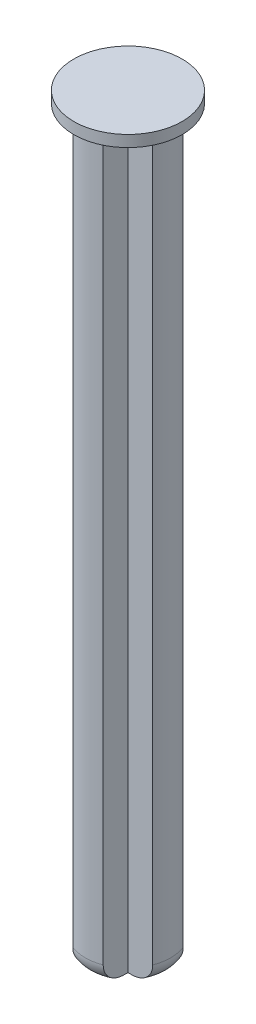
SolidWorks part; units mm, degrees
ref_plane "Front Plane" through (0, 0, 0) normal (0, 0, 1) x (1, 0, 0)
ref_plane "Top Plane" through (0, 0, 0) normal (0, 1, 0) x (1, 0, 0)
ref_plane "Right Plane" through (0, 0, 0) normal (1, 0, 0) x (0, 0, -1)
sketch "Sketch1" plane through (0, 0, 0) normal (0, 1, 0) x (1, 0, 0)
  line L0 (-0.8, -0.8) -> (-0.8, -2.103)
  line L1 (-0.8, 0.8) -> (-2.103, 0.8)
  line L2 (2.103, 0.8) -> (0.8, 0.8)
  line L3 (2.103, -0.8) -> (0.8, -0.8)
  line L4 (0.8, -0.8) -> (0.8, -2.103)
  line L5 (-0.8, -0.8) -> (-2.103, -0.8)
  line L6 (-7.75, 0) -> (-7.75, 0)
  line L7 (-7.75, 0) -> (-7.75, 0)
  line L8 (-0.8, 2.103) -> (-0.8, 0.8)
  line L9 (0.8, 2.103) -> (0.8, 0.8)
  line L10 (-7.75, 0) -> (-7.75, 0)
  line L11 (7.75, 0) -> (7.75, 0)
  line L12 (7.75, 0) -> (7.75, 0)
  line L13 (7.75, 0) -> (7.75, 0)
  line L14 (7.75, 0) -> (7.75, 0)
  line L15 (-7.75, 0) -> (-7.75, 0)
  line L16 (-8.6621, 8.6621) -> (-8.6621, 8.6621)
  line L17 (-8.6621, -8.6621) -> (-8.6621, -8.6621)
  line L18 (-8.6621, -8.6621) -> (-8.6621, -8.6621)
  line L19 (8.6621, -8.6621) -> (8.6621, -8.6621)
  line L20 (8.6621, -8.6621) -> (8.6621, -8.6621)
  line L21 (8.6621, 8.6621) -> (8.6621, 8.6621)
  line L22 (8.6621, 8.6621) -> (8.6621, 8.6621)
  line L23 (-8.6621, 8.6621) -> (-8.6621, 8.6621)
  arc A0 (-2.103, 0.8) -> (-2.103, -0.8) centre (0, 0) ccw
  arc A1 (0.8, 2.103) -> (-0.8, 2.103) centre (0, 0) ccw
  arc A2 (2.103, -0.8) -> (2.103, 0.8) centre (0, 0) ccw
  arc A3 (-0.8, -2.103) -> (0.8, -2.103) centre (0, 0) ccw
  arc A4 (-7.75, 0) -> (-7.75, 0) centre (-7.75, 0) ccw
  arc A5 (-7.75, 0) -> (7.75, 0) centre (0, 0) ccw
  arc A6 (7.75, 0) -> (7.75, 0) centre (7.75, 0) ccw
  arc A7 (7.75, 0) -> (-7.75, 0) centre (0, 0) ccw
  arc A8 (-8.6621, 8.6621) -> (-8.6621, -8.6621) centre (0, 0) ccw
  arc A9 (-8.6621, -8.6621) -> (8.6621, -8.6621) centre (0, 0) ccw
  arc A10 (8.6621, -8.6621) -> (8.6621, 8.6621) centre (0, 0) ccw
  arc A11 (8.6621, 8.6621) -> (-8.6621, 8.6621) centre (0, 0) ccw
  point P26 (0.8, 0)
  dimension "D1" = 4.5
  dimension "D2" = 10
  dimension "D3" = 10
extrude "Boss-Extrude1" add sketch "Sketch1" along normal offset from surface (39.4 mm away) 39.4 contours L0 A3 L4 L3 A2 L2 L9 A1 L8 L1 A0 L5 up to plane "Top Plane"
fillet "Fillet1" radius 1 1 edges at (-2.25, 0, 0)
fillet "Fillet2" radius 1 1 edges at (0, 0, 2.25)
fillet "Fillet3" radius 1 1 edges at (2.25, 0, 0)
fillet "Fillet4" radius 1 1 edges at (0, 0, -2.25)
sketch "Sketch3" plane through (0, 39.4, 0) normal (0, 1, 0) x (1, 0, 0)
  circle A0 centre (0, 0) radius 2.85
  dimension "D1" = 5.7
extrude "Boss-Extrude2" add sketch "Sketch3" against normal blind 0.6 contours A0
